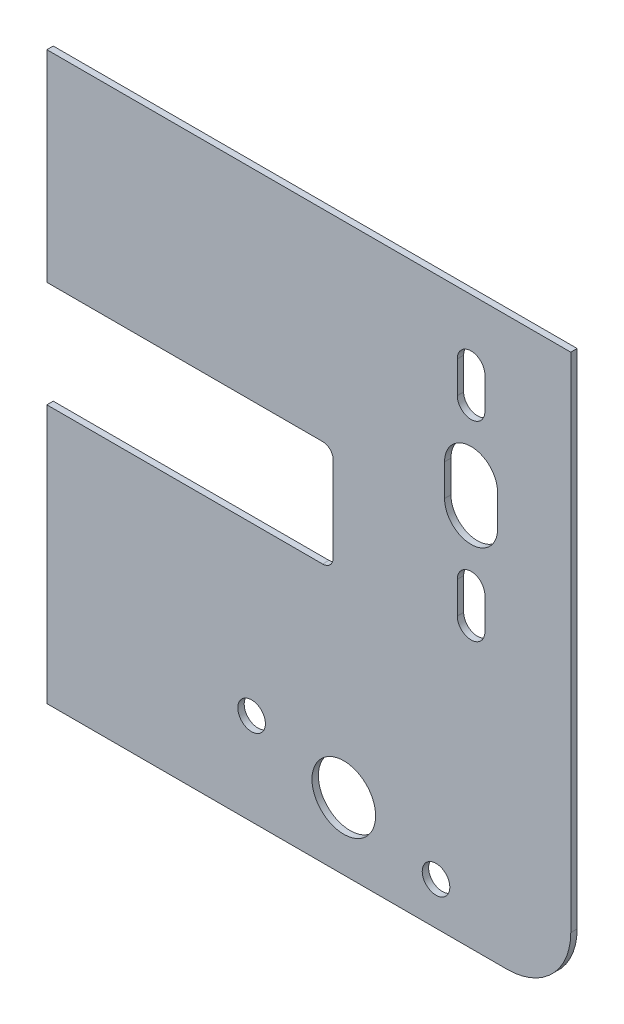
SolidWorks part; units mm, degrees
ref_plane "Plan de face" through (0, 0, 0) normal (0, 0, 1) x (1, 0, 0)
ref_plane "Plan de dessus" through (0, 0, 0) normal (0, 1, 0) x (1, 0, 0)
ref_plane "Plan de droite" through (0, 0, 0) normal (1, 0, 0) x (0, 0, -1)
sketch "Esquisse1" plane through (0, 0, 0) normal (0, 0, 1) x (1, 0, 0)
  line L0 (76.5, 120.5989) -> (76.5, -24.3036) construction
  line L1 (-123.5, -133.5) -> (123.5, -133.5)
  line L2 (-123.5, -133.5) -> (-123.5, 133.5)
  line L3 (-123.5, 133.5) -> (123.5, 133.5)
  line L4 (123.5, -133.5) -> (123.5, 133.5)
  line L5 (-123.5, -133.5) -> (123.5, 133.5) construction
  line L6 (-123.5, 133.5) -> (123.5, -133.5) construction
  circle A0 centre (76.5, 51.5) radius 12.5
  circle A1 centre (76.5, 96.5) radius 6.5
  circle A2 centre (76.5, 6.5) radius 6.5
  point P0 (0, 0)
  dimension "D3" = 25
  dimension "D4" = 13
  dimension "D5" = 13
  dimension "D6" = 90
  dimension "D7" = 45
  dimension "D8" = 200
  dimension "D9" = 82
  dimension "D1" = 247
  dimension "D2" = 267
extrude "Boss.-Extru.1" add sketch "Esquisse1" along normal blind 3
sketch "Esquisse2" plane through (0, 0, 3) normal (0, 0, 1) x (1, 0, 0)
  line L6 (-123.5, 133.5) -> (-123.5, -133.5) construction
  line L11 (-123.5, 48.5) -> (-120.5, 48.5)
  line L12 (-123.5, 48.5) -> (-123.5, -41.5)
  line L13 (-123.5, -41.5) -> (-120.5, -41.5)
  line L14 (-120.5, 48.5) -> (-120.5, -41.5)
  line L15 (123.5, 133.5) -> (-123.5, 133.5) construction
  line L17 (-123.5, 133.5) -> (-48.5, 133.5)
  line L18 (-123.5, 133.5) -> (-123.5, 130.5)
  line L19 (-123.5, 130.5) -> (-48.5, 130.5)
  line L20 (-48.5, 133.5) -> (-48.5, 130.5)
  line L21 (123.5, 133.5) -> (48.5, 133.5)
  line L22 (123.5, 133.5) -> (123.5, 130.5)
  line L23 (123.5, 130.5) -> (48.5, 130.5)
  line L24 (48.5, 133.5) -> (48.5, 130.5)
  dimension "D1" = 3
  dimension "D2" = 85
  dimension "D3" = 90
  dimension "D4" = 3
  dimension "D5" = 75
  dimension "D6" = 75
extrude "Enlèv. mat.-Extru.1" [suppressed] cut sketch "Esquisse2" against normal blind 3
sketch "Esquisse3" plane through (0, 0, 0) normal (0, 0, -1) x (-1, 0, 0)
  line L0 (-70.8887, -116.4266) -> (18.4777, -92.4809) construction
  line L1 (123.5, -133.5) -> (-123.5, -133.5) construction
  line L2 (123.5, 133.5) -> (123.5, -133.5) construction
  circle A0 centre (-59.9667, -113.5) radius 6.5
  circle A1 centre (-16.5, -101.8531) radius 15
  circle A2 centre (26.9667, -90.2063) radius 6.5
  dimension "D1" = 13
  dimension "D2" = 30
  dimension "D3" = 45
  dimension "D4" = 90
  dimension "D5" = 20
  dimension "D6" = 15
  dimension "D7" = 140
extrude "Enlèv. mat.-Extru.2" cut sketch "Esquisse3" against normal blind 3
sketch "Esquisse4" plane through (0, 0, 0) normal (0, 0, -1) x (-1, 0, 0)
  line L0 (123.5, 133.5) -> (123.5, -133.5) construction
  line L1 (123.5, -11.5) -> (-11.5, -11.5)
  line L2 (123.5, -11.5) -> (123.5, 38.5)
  line L3 (123.5, 38.5) -> (-11.5, 38.5)
  line L4 (-11.5, -11.5) -> (-11.5, 38.5)
  line L5 (156.5, -31.5) -> (-673.5, -31.5) construction
  dimension "D1" = 20
  dimension "D2" = 50
  dimension "D3" = 135
extrude "Enlèv. mat.-Extru.3" cut sketch "Esquisse4" against normal blind 10
fillet "Congé1" radius 5 2 edges at (11.5, -11.5, 1.5) (11.5, 38.5, 1.5)
fillet "Congé2" radius 30 1 edges at (123.5, -133.5, 1.5)
sketch "Esquisse5" plane through (0, 0, 0) normal (0, 0, -1) x (-1, 0, 0)
  line L0 (-76.5, 89) -> (-76.5, 104) construction
  line L1 (-83, 89) -> (-83, 104)
  line L2 (-70, 89) -> (-70, 104)
  line L3 (-76.5, -1) -> (-76.5, 14) construction
  line L4 (-83, -1) -> (-83, 14)
  line L5 (-70, -1) -> (-70, 14)
  line L6 (-76.5, 44) -> (-76.5, 59) construction
  line L7 (-89, 44) -> (-89, 59)
  line L8 (-64, 44) -> (-64, 59)
  arc A0 (-83, 89) -> (-70, 89) centre (-76.5, 89) ccw
  arc A1 (-70, 104) -> (-83, 104) centre (-76.5, 104) ccw
  arc A2 (-83, -1) -> (-70, -1) centre (-76.5, -1) ccw
  arc A3 (-70, 14) -> (-83, 14) centre (-76.5, 14) ccw
  arc A4 (-89, 44) -> (-64, 44) centre (-76.5, 44) ccw
  arc A5 (-64, 59) -> (-89, 59) centre (-76.5, 59) ccw
  point P2 (-76.5, 96.5)
  point P10 (-76.5, 6.5)
  point P18 (-76.5, 51.5)
  dimension "D1" = 6.5
  dimension "D3" = 6.5
  dimension "D6" = 12.5
  dimension "D2" = 15
  dimension "D4" = 15
  dimension "D5" = 15
extrude "Enlèv. mat.-Extru.4" cut sketch "Esquisse5" against normal blind 10
